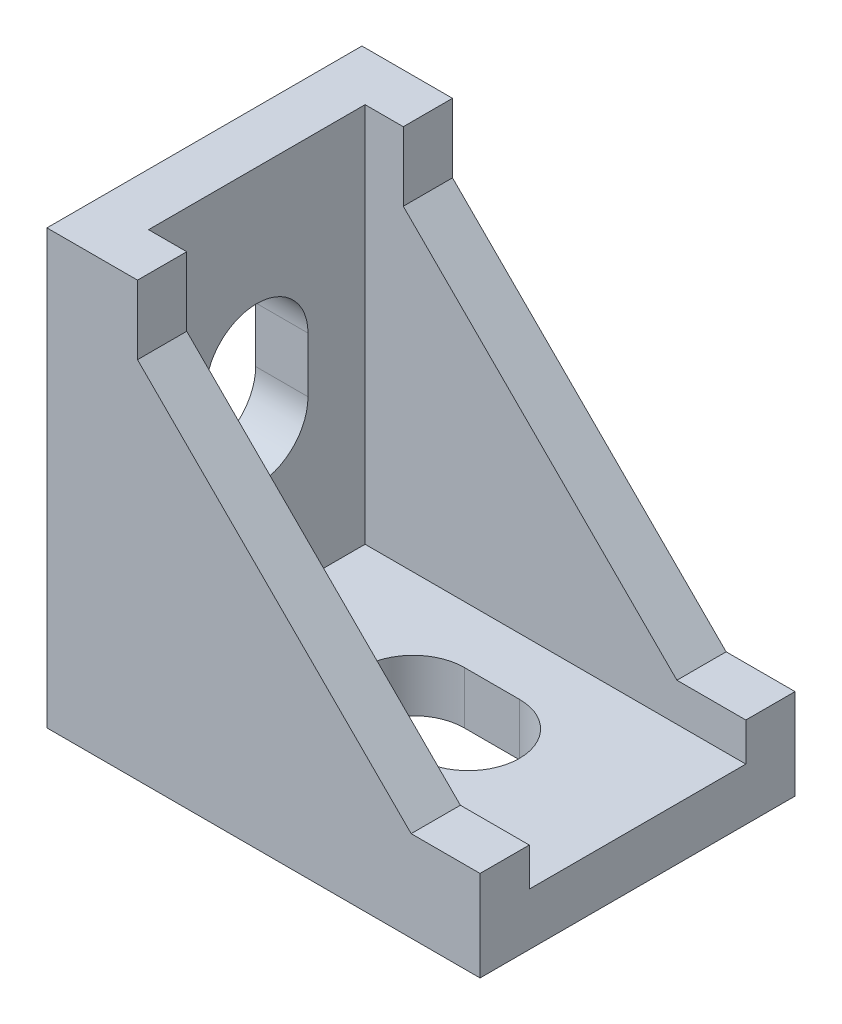
SolidWorks part; units mm, degrees
ref_plane "Front Plane" through (0, 0, 0) normal (0, 0, 1) x (1, 0, 0)
ref_plane "Top Plane" through (0, 0, 0) normal (0, 1, 0) x (1, 0, 0)
ref_plane "Right Plane" through (0, 0, 0) normal (1, 0, 0) x (0, 0, -1)
sketch "Sketch1" plane through (0, 0, 0) normal (0, 0, 1) x (1, 0, 0)
  line L0 (0, 0) -> (0, 27.94)
  line L1 (0, 27.94) -> (5.842, 27.94)
  line L2 (5.842, 27.94) -> (5.842, 23.495)
  line L3 (5.842, 23.495) -> (23.495, 5.842)
  line L4 (23.495, 5.842) -> (27.94, 5.842)
  line L5 (27.94, 5.842) -> (27.94, 0)
  line L6 (27.94, 0) -> (0, 0)
  point P5 (5.842, 20.5229)
  dimension "D1" = 5.842
  dimension "D2" = 27.94
  dimension "D3" = 4.445
extrude "Boss-Extrude1" add sketch "Sketch1" against normal blind 20.32
sketch "Sketch2" plane through (0, 27.94, 0) normal (0, 1, 0) x (1, 0, 0)
  line L1 (3.3782, 17.145) -> (27.94, 17.145)
  line L2 (3.3782, 17.145) -> (3.3782, 3.175)
  line L3 (3.3782, 3.175) -> (27.94, 3.175)
  line L4 (27.94, 17.145) -> (27.94, 3.175)
  line L5 (27.94, 20.32) -> (27.94, 0) construction
  line L6 (0, 20.32) -> (0, 0) construction
  line L7 (5.842, 20.32) -> (0, 20.32) construction
  line L8 (5.842, 0) -> (0, 0) construction
  dimension "D1" = 3.3782
  dimension "D2" = 3.175
  dimension "D3" = 3.175
extrude "Cut-Extrude1" cut sketch "Sketch2" against normal offset from surface (24.5618 mm away) 3.3782 up to face at (13.97, 0, -10.16)
sketch "Sketch3" plane through (0, 3.3782, 0) normal (0, 1, 0) x (1, 0, 0)
  line L0 (13.462, 10.16) -> (17.018, 10.16) construction
  line L1 (13.462, 13.462) -> (17.018, 13.462)
  line L2 (13.462, 6.858) -> (17.018, 6.858)
  line L3 (27.94, 3.175) -> (27.94, 17.145) construction
  arc A0 (13.462, 13.462) -> (13.462, 6.858) centre (13.462, 10.16) ccw
  arc A1 (17.018, 6.858) -> (17.018, 13.462) centre (17.018, 10.16) ccw
  point P2 (15.24, 10.16)
  point P9 (27.94, 10.16)
  point P10 (10.16, 10.16)
  point P11 (20.32, 10.16)
  dimension "D1" = 10.16
  dimension "D2" = 7.62
  dimension "D3" = 6.604
extrude "Cut-Extrude2" cut sketch "Sketch3" against normal through all
pattern_circular "CirPattern1" count 2 over 270 about axis through (0, 0, -20.32) along (0, 0, 1) of "Cut-Extrude2"
